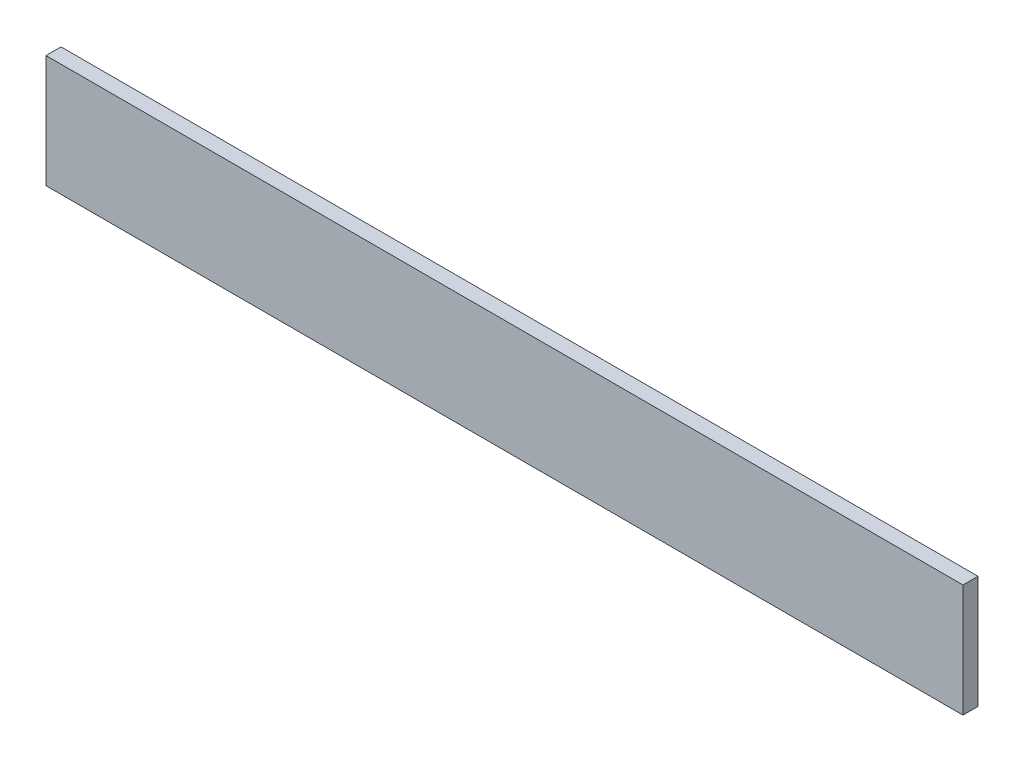
SolidWorks part; units mm, degrees
ref_plane "Front Plane" through (0, 0, 0) normal (0, 0, 1) x (1, 0, 0)
ref_plane "Top Plane" through (0, 0, 0) normal (0, 1, 0) x (1, 0, 0)
ref_plane "Right Plane" through (0, 0, 0) normal (1, 0, 0) x (0, 0, -1)
sketch "Sketch1" plane through (0, 0, 0) normal (0, 0, 1) x (1, 0, 0)
  line L1 (0, 0) -> (122, 0)
  line L2 (0, 0) -> (0, 15)
  line L3 (0, 15) -> (122, 15)
  line L4 (122, 0) -> (122, 15)
  dimension "D1" = 122
  dimension "D2" = 15
extrude "Boss-Extrude1" add sketch "Sketch1" along normal blind 2
